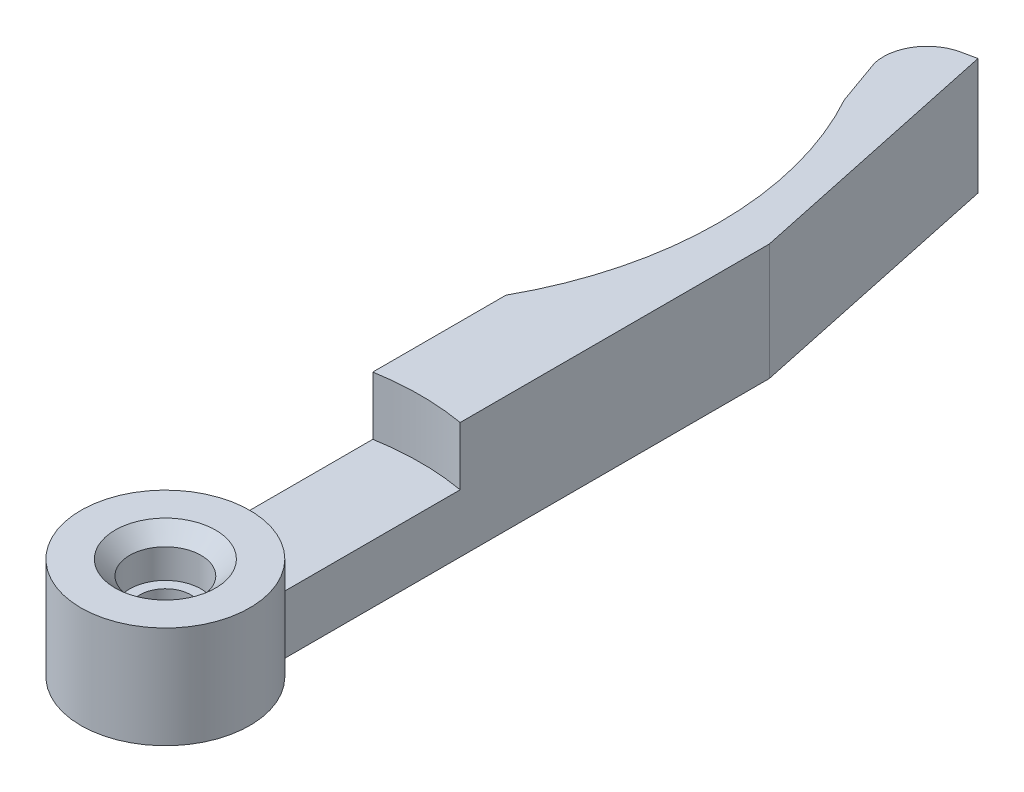
SolidWorks part; units mm, degrees
other "Marquage1"
sketch "Esquisse6" plane through (-5.8, 8, 5.8) normal (-0.828, 0.5586, 0.0482) x (0.5598, 0.8285, 0.0157)
ref_plane "Plan de face" through (0, 0, 0) normal (0, 0, 1) x (1, 0, 0)
ref_plane "Plan de dessus" through (0, 0, 0) normal (0, 1, 0) x (1, 0, 0)
ref_plane "Plan de droite" through (0, 0, 0) normal (1, 0, 0) x (0, 0, -1)
sketch "Esquisse1" plane through (0, 0, 0) normal (0, 1, 0) x (1, 0, 0)
  line L0 (-3, 50.619) -> (-3, 49.619) construction
  line L1 (2, 55.619) -> (3, 55.619) construction
  line L2 (-3, 55.619) -> (-3, 4.9639) construction
  line L3 (-3, 4.9639) -> (3, 4.9639) construction
  line L4 (3, 55.619) -> (3, 4.9639) construction
  line L5 (-3, 26.381) -> (-3, 4.9639)
  line L7 (-3, 4.9639) -> (3, 4.9639) construction
  line L12 (0, 4.9639) -> (0, -14.5149) construction
  line L13 (-4.1404, 52.822) -> (-3, 49.619)
  line L14 (-1.8453, 56.4495) -> (-0.8672, 56.6574)
  line L15 (-0.8672, 56.6574) -> (3, 38.4639)
  line L16 (3, 38.4639) -> (3, 4.9639)
  arc A0 (-3, 49.619) -> (-3, 26.381) centre (-24, 38) cw
  arc A1 (2, 55.619) -> (-3, 50.619) centre (2, 50.619) ccw construction
  circle A2 centre (0, 0) radius 2.4 construction
  arc A3 (-4.1404, 52.822) -> (-1.8453, 56.4495) centre (-1.2216, 53.5151) cw
  arc A4 (-3, 4.9639) -> (3, 4.9639) centre (0, 0) ccw
  point P19 (0, 38)
  point P25 (-4.3024, 55.9871)
  dimension "D2" = 24
  dimension "D5" = 5
  dimension "D10" = 3
  dimension "D7" = 4.8
  dimension "D11" = 5.8
  dimension "D1" = 6
  dimension "D3" = 21
  dimension "D4" = 6
  dimension "D6" = 38
  dimension "D8" = 3.5
  dimension "D9" = 6.5
  dimension "D12" = 33.5
  dimension "D13" = 12
  dimension "D14" = 18.6
  dimension "D15" = 3.4
  dimension "D16" = 1
extrude "Boss.-Extru.1" add sketch "Esquisse1" along normal blind 8
sketch "Esquisse2" plane through (0, 8, 0) normal (0, 1, 0) x (1, 0, 0)
  line L0 (0, 38) -> (0, 0) construction
  circle A0 centre (0, 0) radius 2.45
  arc A1 (-3, 26.381) -> (-3, 49.619) centre (-24, 38) ccw construction
  dimension "D2" = 4.9
  dimension "D1" = 38
extrude "Enlèv. mat.-Extru.1" cut sketch "Esquisse2" against normal blind 4
sketch "Esquisse3" plane through (0, 4, 0) normal (0, 1, 0) x (1, 0, 0)
  circle A0 centre (0, 0) radius 1.75
  dimension "D1" = 3.5
extrude "Enlèv. mat.-Extru.2" cut sketch "Esquisse3" against normal up to next
sketch "Esquisse4" plane through (0, 0, 0) normal (0, -1, 0) x (1, 0, 0)
  circle A0 centre (0, 0) radius 3.75
  dimension "D1" = 7.5
extrude "Enlèv. mat.-Extru.3" cut sketch "Esquisse4" against normal blind 2.5
sketch "Esquisse5" plane through (0, 8, 0) normal (0, 1, 0) x (1, 0, 0)
  line L0 (-3, 4.9639) -> (-3, 17.2409)
  line L1 (3, 4.9639) -> (3, 17.2409)
  line L2 (3, 4.9639) -> (3, 38.4639) construction
  circle A0 centre (0, 0) radius 5.8 construction
  circle A1 centre (0, 0) radius 17.5 construction
  arc A2 (-3, 4.9639) -> (3, 4.9639) centre (0, 0) ccw construction
  arc A3 (-3, 4.9639) -> (3, 4.9639) centre (0, 0) cw
  arc A4 (-3, 17.2409) -> (3, 17.2409) centre (0, 0) cw
  dimension "D1" = 35
extrude "Enlèv. mat.-Extru.4" cut sketch "Esquisse5" against normal blind 4
sketch "Esquisse7" plane through (0, 8, 0) normal (0, 1, 0) x (1, 0, 0)
  circle A0 centre (0, 0) radius 5.8
extrude "Enlèv. mat.-Extru.5" cut sketch "Esquisse7" against normal blind 1
chamfer "Chanfrein1" distance 1 angle 45 1 edges at (0, 7, 2.45)
